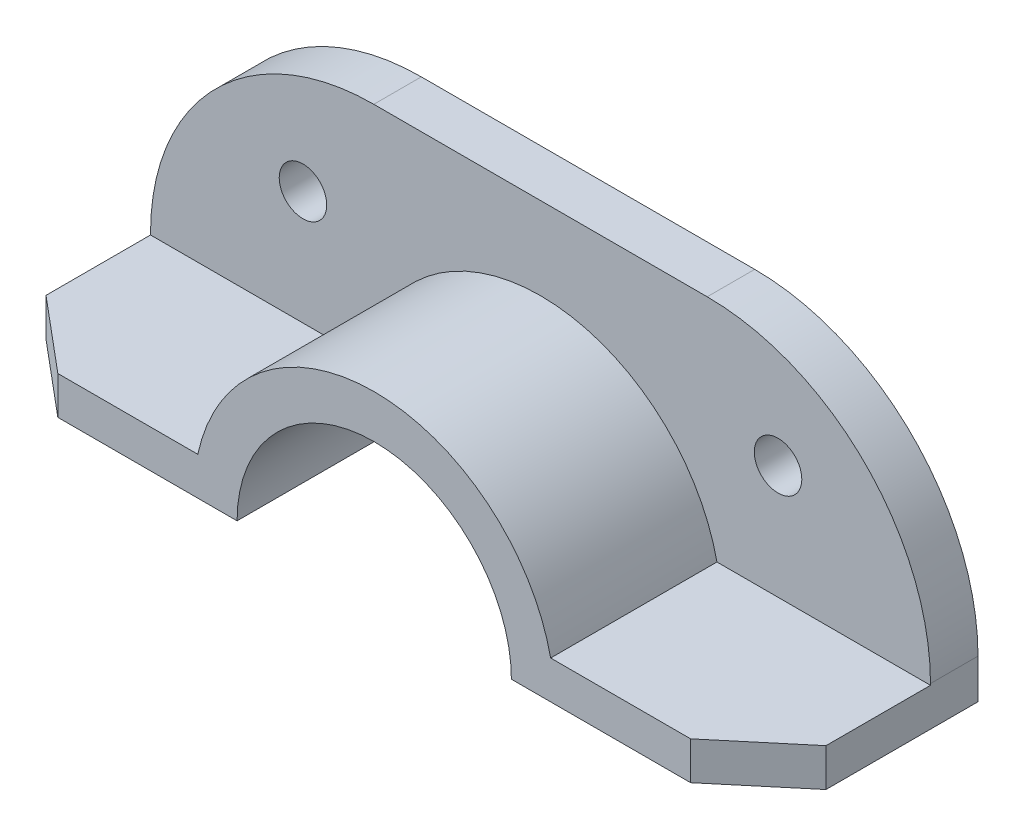
SolidWorks part; units mm, degrees
ref_plane "Piano frontale" through (0, 0, 0) normal (0, 0, 1) x (1, 0, 0)
ref_plane "Piano superiore" through (0, 0, 0) normal (0, 1, 0) x (1, 0, 0)
ref_plane "Piano destro" through (0, 0, 0) normal (1, 0, 0) x (0, 0, -1)
sketch "Schizzo1" plane through (0, 0, 0) normal (0, 0, 1) x (1, 0, 0)
  line L0 (28.8691, 0) -> (82.0882, 0)
  line L1 (55, 0) -> (-55, 0) construction
  line L2 (82.0882, 0) -> (82.0882, 8)
  line L3 (82.0882, 8) -> (37.1347, 8)
  line L5 (0, -55) -> (0, 55) construction
  line L6 (0, 28.8691) -> (0, 37.9866)
  arc A0 (37.1347, 8) -> (0, 37.9866) centre (0, 0) ccw
  arc A1 (28.8691, 0) -> (0, 28.8691) centre (0, 0) ccw
  point P8 (33.0535, 8.4432)
  point P9 (28.1214, 0)
  point P10 (37.8154, 10.314)
  point P13 (0, 0)
  dimension "D2" = 28.8691
  dimension "D3" = 37.9866
  dimension "D1" = 8
  dimension "D4" = 82.0882
extrude "Estrusione-Estrusione1" add sketch "Schizzo1" along normal mid plane 40
sketch "Schizzo3" plane through (0, 0, -20) normal (0, 0, -1) x (-1, 0, 0)
  line L0 (-82.0882, 0) -> (-82.0882, 55.3264) construction
  line L1 (22, 0) -> (-22, 0) construction
  line L2 (-82.0882, 0) -> (-82.0882, 8) construction
  line L3 (-82.0882, 55.3264) -> (0, 55.3264) construction
  line L4 (0, 22) -> (0, -22) construction
  line L5 (0, 55.3264) -> (0, 0) construction
  line L6 (0, 0) -> (-82.0882, 0) construction
  dimension "D1" = 55.3264
sketch "Schizzo4" plane through (0, 0, -20) normal (0, 0, -1) x (-1, 0, 0)
  line L0 (-28.8691, 0) -> (-82.0882, 0)
  line L1 (-82.0882, 0) -> (-82.0882, 55.3264)
  line L2 (-82.0882, 55.3264) -> (0, 55.3264)
  line L3 (0, 55.3264) -> (0, 28.8691)
  arc A0 (0, 28.8691) -> (-28.8691, 0) centre (0, 0) ccw
  dimension "D1" = 28.8691
extrude "Estrusione-Estrusione3" add sketch "Schizzo4" along normal mid plane 10
fillet "Raccordo1" radius 47 1 edges at (82.0882, 55.3264, -20)
sketch "Schizzo5" plane through (0, 0, -15) normal (0, 0, 1) x (1, 0, 0)
  line L0 (37.1347, 8) -> (82.0882, 8) construction
  line L1 (0, 55.3264) -> (0, 0) construction
  circle A0 centre (50, 32) radius 5
  dimension "D1" = 10
  dimension "D2" = 24
  dimension "D3" = 50
extrude "Taglio-Estrusione1" cut sketch "Schizzo5" against normal blind 10
sketch "Schizzo6" plane through (0, 8, 0) normal (0, 1, 0) x (1, 0, 0)
  line L0 (66.5954, -20) -> (82.0882, -7)
  line L1 (82.0882, -20) -> (37.1347, -20) construction
  line L2 (82.0882, -20) -> (82.0882, 15) construction
  line L3 (82.0882, -7) -> (82.0882, -20)
  line L4 (82.0882, -20) -> (66.5954, -20)
  point P6 (65.8721, -20)
  dimension "D1" = 40
  dimension "D2" = 13
extrude "Taglio-Estrusione2" cut sketch "Schizzo6" against normal blind 10
mirror "Specchia2" about plane through (0, 0, 0) normal (1, 0, 0) of "Taglio-Estrusione2", "Taglio-Estrusione1", "Raccordo1", "Estrusione-Estrusione3", "Estrusione-Estrusione1"
